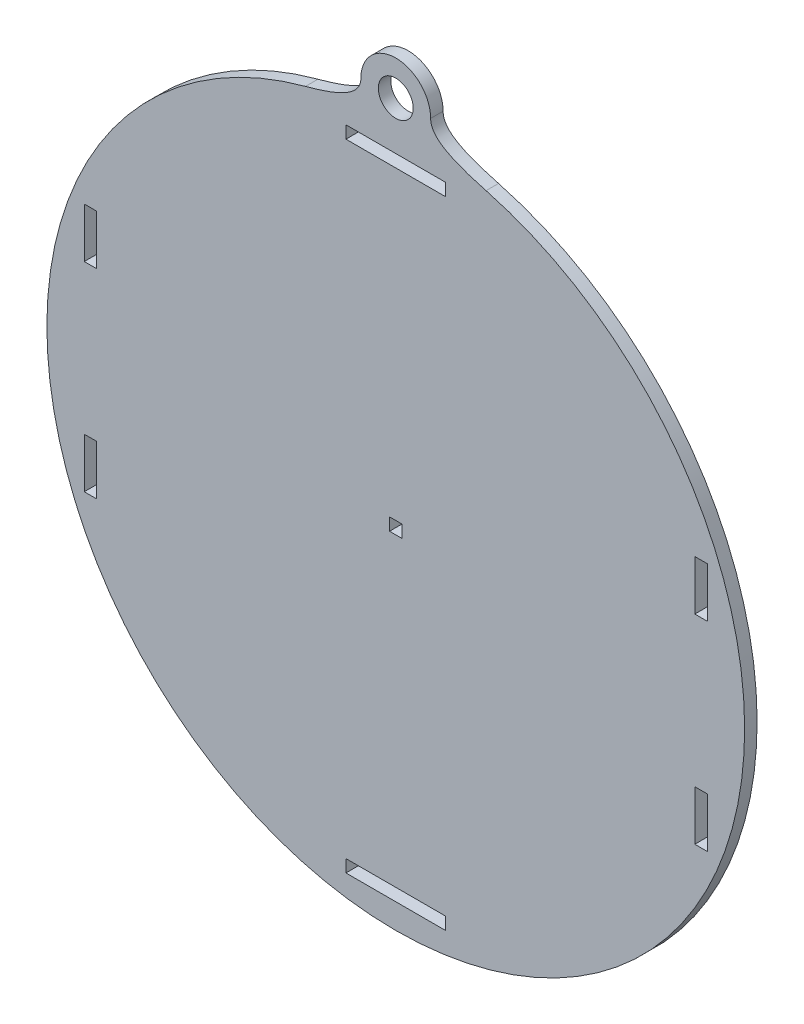
SolidWorks part; units mm, degrees
ref_plane "Front Plane" through (0, 0, 0) normal (0, 0, 1) x (1, 0, 0)
ref_plane "Top Plane" through (0, 0, 0) normal (0, 1, 0) x (1, 0, 0)
ref_plane "Right Plane" through (0, 0, 0) normal (1, 0, 0) x (0, 0, -1)
sketch "Sketch1" plane through (0, 0, 0) normal (0, 0, 1) x (1, 0, 0)
  line L0 (79.375, 31.7348) -> (76.2, 31.7348)
  line L1 (-1.5875, -1.5875) -> (1.5875, -1.5875)
  line L2 (-1.5875, -1.5875) -> (-1.5875, 1.5875)
  line L3 (-1.5875, 1.5875) -> (1.5875, 1.5875)
  line L4 (1.5875, -1.5875) -> (1.5875, 1.5875)
  line L5 (-1.5875, -1.5875) -> (1.5875, 1.5875) construction
  line L6 (-1.5875, 1.5875) -> (1.5875, -1.5875) construction
  line L7 (79.375, 31.7348) -> (79.375, 19.0348)
  line L8 (76.2, 31.7348) -> (76.2, 19.0348)
  line L9 (79.375, 19.0348) -> (76.2, 19.0348)
  line L10 (79.375, -19.0652) -> (76.2, -19.0652)
  line L11 (79.375, -19.0652) -> (79.375, -31.7652)
  line L12 (76.2, -19.0652) -> (76.2, -31.7652)
  line L13 (79.375, -31.7652) -> (76.2, -31.7652)
  line L14 (79.375, -31.7652) -> (76.2, -31.7652) construction
  line L15 (79.375, 19.0348) -> (76.2, 19.0348) construction
  line L16 (0, -1000) -> (0, 49000) construction
  line L17 (-79.375, -31.7652) -> (-76.2, -31.7652)
  line L18 (-76.2, -19.0652) -> (-76.2, -31.7652)
  line L19 (-79.375, -19.0652) -> (-79.375, -31.7652)
  line L20 (-79.375, -19.0652) -> (-76.2, -19.0652)
  line L21 (-79.375, 19.0348) -> (-76.2, 19.0348)
  line L22 (-76.2, 31.7348) -> (-76.2, 19.0348)
  line L23 (-79.375, 31.7348) -> (-79.375, 19.0348)
  line L24 (-79.375, 31.7348) -> (-76.2, 31.7348)
  line L25 (-12.7, 82.55) -> (-12.7, 79.375)
  line L26 (-12.7, 82.55) -> (12.7, 82.55)
  line L27 (-12.7, 79.375) -> (12.7, 79.375)
  line L28 (12.7, 82.55) -> (12.7, 79.375)
  line L29 (-12.7, -79.375) -> (-12.7, -82.55)
  line L30 (-12.7, -79.375) -> (12.7, -79.375)
  line L31 (-12.7, -82.55) -> (12.7, -82.55)
  line L32 (12.7, -79.375) -> (12.7, -82.55)
  line L33 (12.7, -82.55) -> (12.7, -79.375) construction
  line L34 (12.7, 82.55) -> (12.7, 79.375) construction
  line L35 (69.0228, 73.5414) -> (127.0918, 57.9819) construction
  line L36 (8.89, -34.9971) -> (8.89, -40.7365) construction
  line L37 (86.1498, 115.1198) -> (41.4139, 103.1329) construction
  line L38 (30.7404, 100.2729) -> (-78.6835, 70.9529) construction
  line L39 (-30.1441, 100.1131) -> (79.2799, 70.7931) construction
  arc A0 (-23.009, 85.8708) -> (23.009, 85.8708) centre (0, 0) ccw
  arc A1 (-8.89, 94.7608) -> (8.89, 94.7608) centre (0, 94.7608) cw
  circle A2 centre (0, 94.7608) radius 4.445
  spline S0 degree 3 poles (-23.009, 85.8708) (-14.8308, 88.0621) (-8.89, 90.5275) (-8.89, 94.7608) knots 0 0 0 0 1 1 1 1
  spline S1 degree 3 poles (23.009, 85.8708) (14.8308, 88.0621) (8.89, 90.5275) (8.89, 94.7608) knots 0 0 0 0 1 1 1 1
  dimension "D1" = 177.8
  dimension "D4" = 8.89
  dimension "D5" = 25.4
  dimension "D6" = 25.4
  dimension "D9" = 12.7
  dimension "D10" = 12.7
  dimension "D11" = 4.445
  dimension "D12" = 8.89
  dimension "D13" = 8.89
  dimension "D2" = 3.175
  dimension "D3" = 3.175
  dimension "D7" = 105
  dimension "D8" = 105
extrude "Boss-Extrude1" add sketch "Sketch1" along normal blind 3.175
